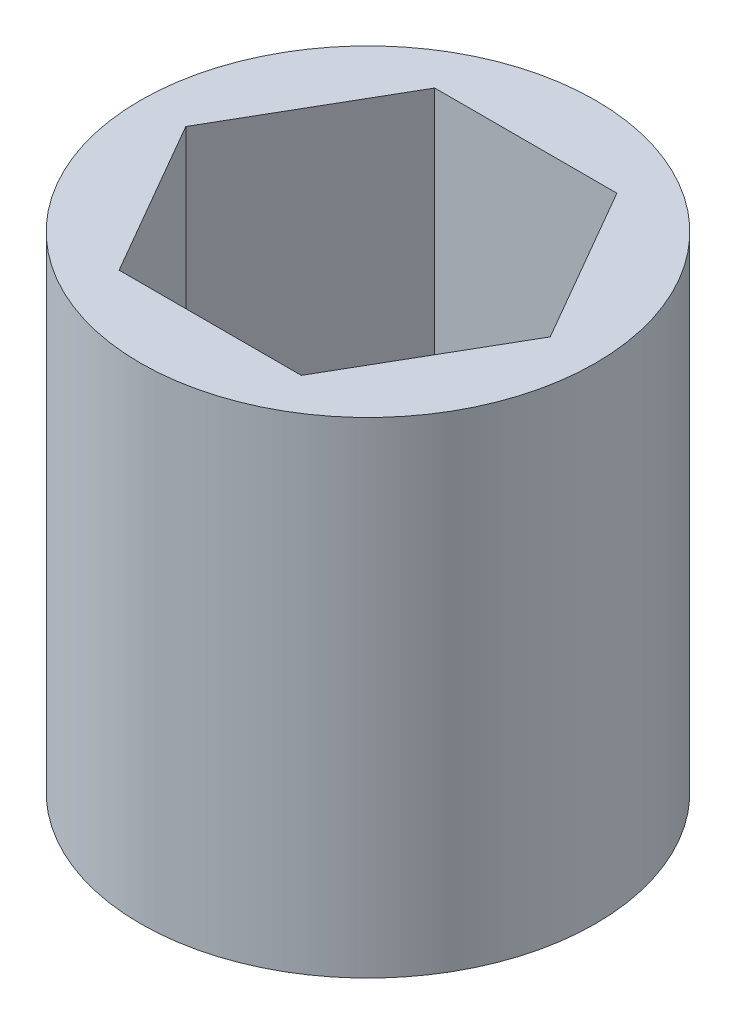
SolidWorks part; units mm, degrees
material "ABS"
ref_plane "Front Plane" through (0, 0, 0) normal (0, 0, 1) x (1, 0, 0)
ref_plane "Top Plane" through (0, 0, 0) normal (0, 1, 0) x (1, 0, 0)
ref_plane "Right Plane" through (0, 0, 0) normal (1, 0, 0) x (0, 0, -1)
sketch "Sketch1" plane through (0, 0, 0) normal (0, 1, 0) x (1, 0, 0)
  line L1 (3.8128, 6.604) -> (-3.8128, 6.604)
  line L2 (-3.8128, 6.604) -> (-7.6256, 0)
  line L3 (-7.6256, 0) -> (-3.8128, -6.604)
  line L4 (-3.8128, -6.604) -> (3.8128, -6.604)
  line L5 (3.8128, -6.604) -> (7.6256, 0)
  line L6 (7.6256, 0) -> (3.8128, 6.604)
  circle A0 centre (0, 0) radius 6.604 construction
  circle A1 centre (0, 0) radius 9.525
  dimension "D1" = 13.208
  dimension "D2" = 19.05
extrude "Boss-Extrude1" add sketch "Sketch1" along normal blind 20.32
